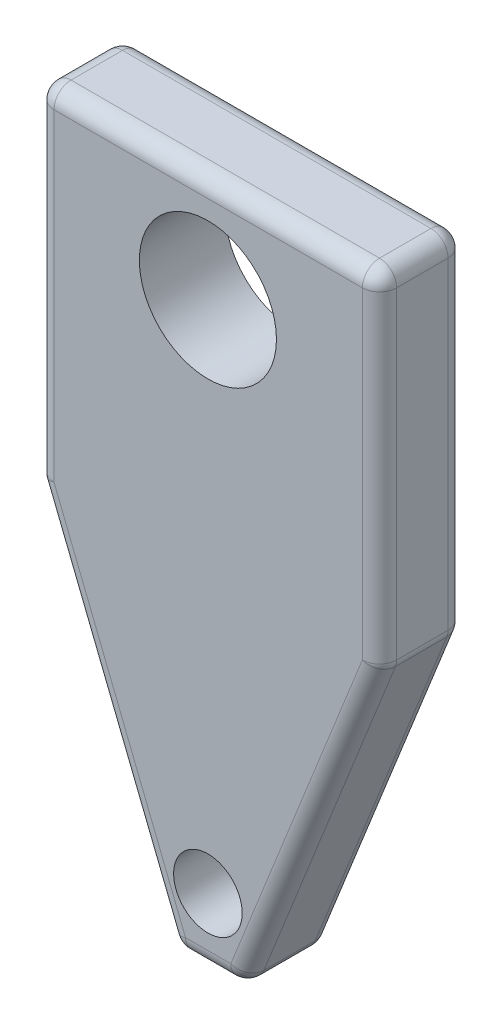
SolidWorks part; units mm, degrees
ref_plane "Front Plane" through (0, 0, 0) normal (0, 0, 1) x (1, 0, 0)
ref_plane "Top Plane" through (0, 0, 0) normal (0, 1, 0) x (1, 0, 0)
ref_plane "Right Plane" through (0, 0, 0) normal (1, 0, 0) x (0, 0, -1)
sketch "Sketch1" plane through (0, 0, 0) normal (0, 0, 1) x (1, 0, 0)
  line L0 (0, -20) -> (8, -40)
  line L1 (0, 0) -> (20, 0)
  line L2 (0, 0) -> (0, -20)
  line L3 (8, -40) -> (12, -40)
  line L4 (20, 0) -> (20, -20)
  line L5 (20, -20) -> (12, -40)
  circle A0 centre (9.9846, -6.1149) radius 4
  circle A1 centre (9.9846, -36.1149) radius 2
  dimension "D5" = 8
  dimension "D6" = 4
  dimension "D1" = 20
  dimension "D7" = 30
extrude "Boss-Extrude1" add sketch "Sketch1" along normal blind 5
fillet "Fillet1" radius 1 18 edges at (4, -30, 5) (8, -40, 2.5) (4, -30, 0) (0, -10, 5) (0, -20, 2.5) (0, -10, 0) (12, -40, 2.5) (16, -30, 5) (16, -30, 0) (20, -20, 2.5) (20, -10, 5) (20, -10, 0) (20, 0, 2.5) (10, 0, 5) (0, 0, 2.5) (10, 0, 0) (10, -40, 0) (10, -40, 5)
